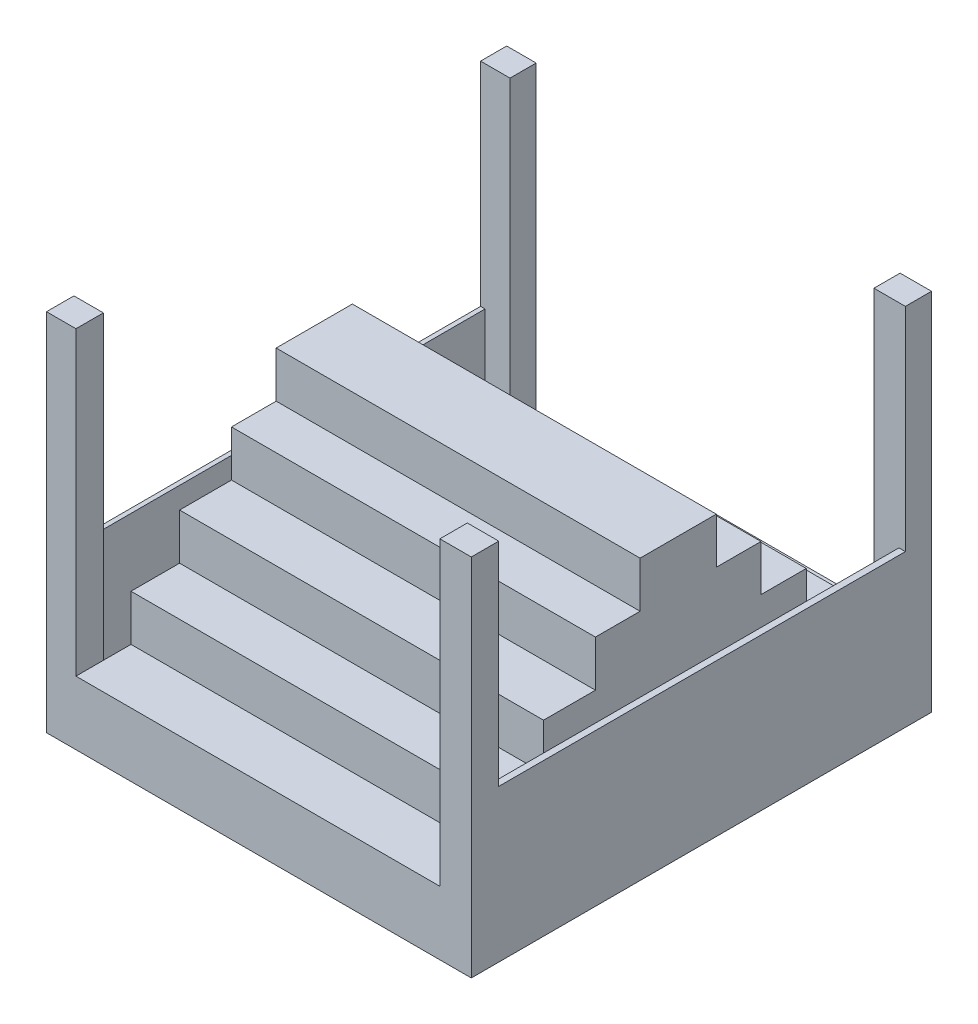
SolidWorks part; units mm, degrees
ref_plane "Alzado" through (0, 0, 0) normal (0, 0, 1) x (1, 0, 0)
ref_plane "Planta" through (0, 0, 0) normal (0, 1, 0) x (1, 0, 0)
ref_plane "Vista lateral" through (0, 0, 0) normal (1, 0, 0) x (0, 0, -1)
sketch "Croquis1" plane through (0, 0, 0) normal (0, 1, 0) x (1, 0, 0)
  line L1 (0, 0) -> (1200, 0)
  line L2 (0, 0) -> (0, 1300)
  line L3 (0, 1300) -> (1200, 1300)
  line L4 (1200, 0) -> (1200, 1300)
  dimension "D1" = 1300
  dimension "D2" = 1200
extrude "Saliente-Extruir1" add sketch "Croquis1" along normal blind 30
sketch "Croquis2" plane through (0, 30, 0) normal (0, 1, 0) x (1, 0, 0)
  line L1 (0, 1300) -> (83.2029, 1300)
  line L2 (0, 1300) -> (0, 1226.1777)
  line L3 (0, 1226.1777) -> (83.2029, 1226.1777)
  line L4 (83.2029, 1300) -> (83.2029, 1226.1777)
  line L5 (1200, 1300) -> (1111.2302, 1300)
  line L6 (1200, 1300) -> (1200, 1226.1777)
  line L7 (1200, 1226.1777) -> (1111.2302, 1226.1777)
  line L8 (1111.2302, 1300) -> (1111.2302, 1226.1777)
  line L9 (0, 0) -> (83.2029, 0)
  line L10 (0, 0) -> (0, 77.5335)
  line L11 (0, 77.5335) -> (83.2029, 77.5335)
  line L12 (83.2029, 0) -> (83.2029, 77.5335)
  line L13 (1200, 0) -> (1111.2302, 0)
  line L14 (1200, 0) -> (1200, 77.5335)
  line L15 (1200, 77.5335) -> (1111.2302, 77.5335)
  line L16 (1111.2302, 0) -> (1111.2302, 77.5335)
extrude "Saliente-Extruir2" add sketch "Croquis2" along normal blind 1000
sketch "Croquis3" plane through (0, 30, 0) normal (0, 1, 0) x (1, 0, 0)
  line L0 (83.2029, 77.5335) -> (0, 77.5335) construction
  line L1 (0, 1226.1777) -> (12.6884, 1226.1777)
  line L2 (0, 1226.1777) -> (0, 77.5335)
  line L3 (0, 77.5335) -> (12.6884, 77.5335)
  line L4 (12.6884, 1226.1777) -> (12.6884, 77.5335)
  line L5 (1200, 77.5335) -> (1111.2302, 77.5335) construction
  line L6 (1200, 1226.1777) -> (1181.7447, 1226.1777)
  line L7 (1200, 1226.1777) -> (1200, 77.5335)
  line L8 (1200, 77.5335) -> (1181.7447, 77.5335)
  line L9 (1181.7447, 1226.1777) -> (1181.7447, 77.5335)
extrude "Saliente-Extruir3" add sketch "Croquis3" along normal blind 400
sketch "Croquis4" plane through (0, 30, 0) normal (0, 1, 0) x (1, 0, 0)
  line L1 (83.2029, 1300) -> (1111.2302, 1300)
  line L2 (83.2029, 1300) -> (83.2029, 0)
  line L3 (83.2029, 0) -> (1111.2302, 0)
  line L4 (1111.2302, 1300) -> (1111.2302, 0)
extrude "Saliente-Extruir4" add sketch "Croquis4" along normal blind 150
sketch "Croquis5" plane through (0, 180, 0) normal (0, 1, 0) x (1, 0, 0)
  line L0 (83.2029, 1226.1777) -> (83.2029, 77.5335) construction
  line L1 (83.2029, 1161.2302) -> (1111.2302, 1161.2302)
  line L2 (83.2029, 1161.2302) -> (83.2029, 155.4706)
  line L3 (83.2029, 155.4706) -> (1111.2302, 155.4706)
  line L4 (1111.2302, 1161.2302) -> (1111.2302, 155.4706)
  line L5 (1111.2302, 77.5335) -> (1111.2302, 1226.1777) construction
extrude "Saliente-Extruir5" add sketch "Croquis5" along normal blind 130
sketch "Croquis6" plane through (0, 310, 0) normal (0, 1, 0) x (1, 0, 0)
  line L0 (83.2029, 1161.2302) -> (83.2029, 155.4706) construction
  line L1 (83.2029, 1035.0463) -> (1111.2302, 1035.0463)
  line L2 (83.2029, 1035.0463) -> (83.2029, 292.7884)
  line L3 (83.2029, 292.7884) -> (1111.2302, 292.7884)
  line L4 (1111.2302, 1035.0463) -> (1111.2302, 292.7884)
  line L5 (1111.2302, 155.4706) -> (1111.2302, 1161.2302) construction
extrude "Saliente-Extruir6" add sketch "Croquis6" along normal blind 130
sketch "Croquis7" plane through (0, 440, 0) normal (0, 1, 0) x (1, 0, 0)
  line L0 (83.2029, 1035.0463) -> (83.2029, 292.7884) construction
  line L1 (83.2029, 907.0068) -> (1111.2302, 907.0068)
  line L2 (83.2029, 907.0068) -> (83.2029, 439.3843)
  line L3 (83.2029, 439.3843) -> (1111.2302, 439.3843)
  line L4 (1111.2302, 907.0068) -> (1111.2302, 439.3843)
  line L5 (1111.2302, 292.7884) -> (1111.2302, 1035.0463) construction
extrude "Saliente-Extruir7" add sketch "Croquis7" along normal blind 130
sketch "Croquis8" plane through (0, 570, 0) normal (0, 1, 0) x (1, 0, 0)
  line L0 (83.2029, 907.0068) -> (83.2029, 439.3843) construction
  line L1 (83.2029, 780.823) -> (1111.2302, 780.823)
  line L2 (83.2029, 780.823) -> (83.2029, 565.5682)
  line L3 (83.2029, 565.5682) -> (1111.2302, 565.5682)
  line L4 (1111.2302, 780.823) -> (1111.2302, 565.5682)
  line L5 (1111.2302, 77.5335) -> (1111.2302, 1226.1777) construction
extrude "Saliente-Extruir8" add sketch "Croquis8" along normal blind 130
